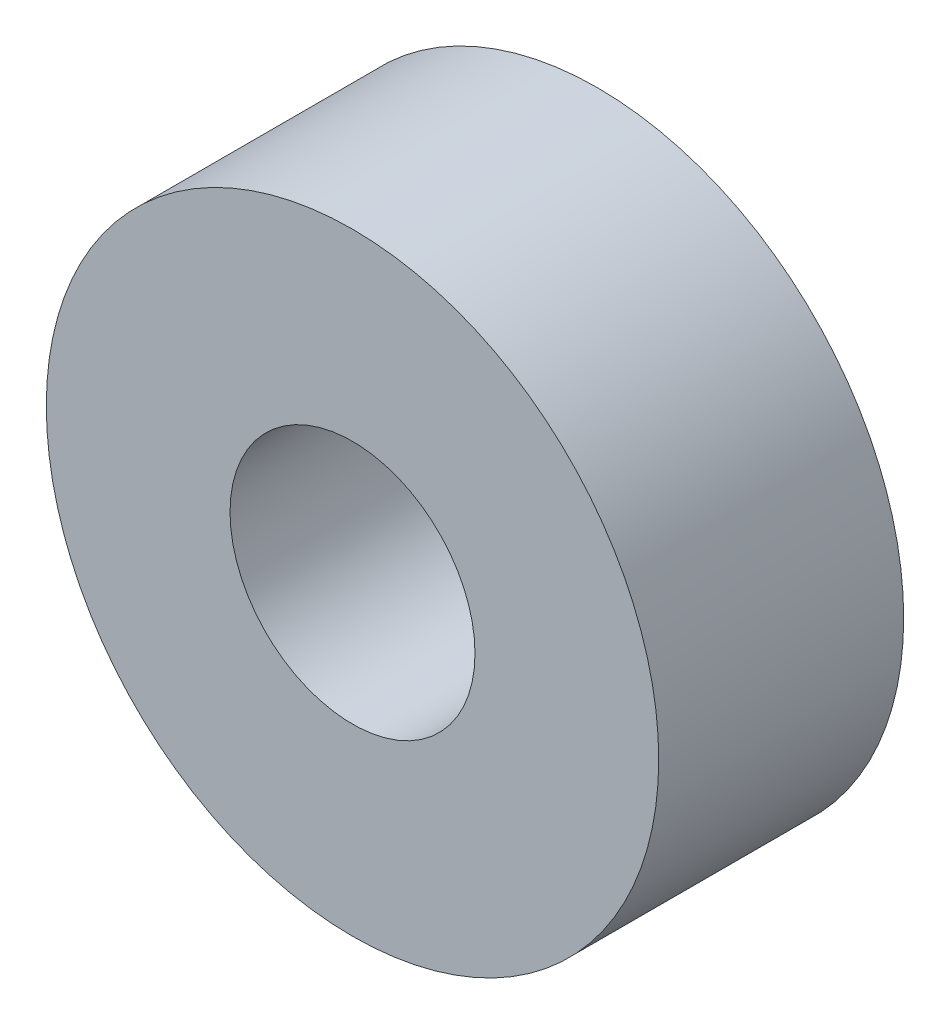
SolidWorks part; units mm, degrees
material "AISI 303 Stainless"
ref_plane "Front Plane" through (0, 0, 0) normal (0, 0, 1) x (1, 0, 0)
ref_plane "Top Plane" through (0, 0, 0) normal (0, 1, 0) x (1, 0, 0)
ref_plane "Right Plane" through (0, 0, 0) normal (1, 0, 0) x (0, 0, -1)
other "Configuration Table"
sketch "Sketch1" plane through (0, 0, 0) normal (0, 0, 1) x (1, 0, 0)
  circle A0 centre (0, 0) radius 3.175
  circle A1 centre (0, 0) radius 7.9375
  dimension "D1" = 6.35
  dimension "D2" = 15.875
extrude "Boss-Extrude1" add sketch "Sketch1" along normal blind 6.35 contours A1
sketch "Sketch2" plane through (0, 0, 6.35) normal (0, 0, 1) x (1, 0, 0)
  point P0 (0, 0)
hole_wizard "1/4 (0.25) Diameter Hole1" positions "Sketch2" profile "Sketch3" hole size "1/4" standard "ANSI Inch" end condition through all
sketch "Sketch3" plane through (0, 0, 6.35) normal (1, 0, 0) x (0, -1, 0)
  line L0 (0, 0) -> (0, 6.35)
  line L1 (0, 6.35) -> (3.175, 6.35)
  line L2 (3.175, 6.35) -> (3.175, 0)
  line L5 (3.175, 0) -> (0, 0)
  line L11 (0, -6.35) -> (0, 107.95) construction
  dimension "Thru Hole Dia." = 6.35
  dimension "Thru Hole Depth" = 6.35
